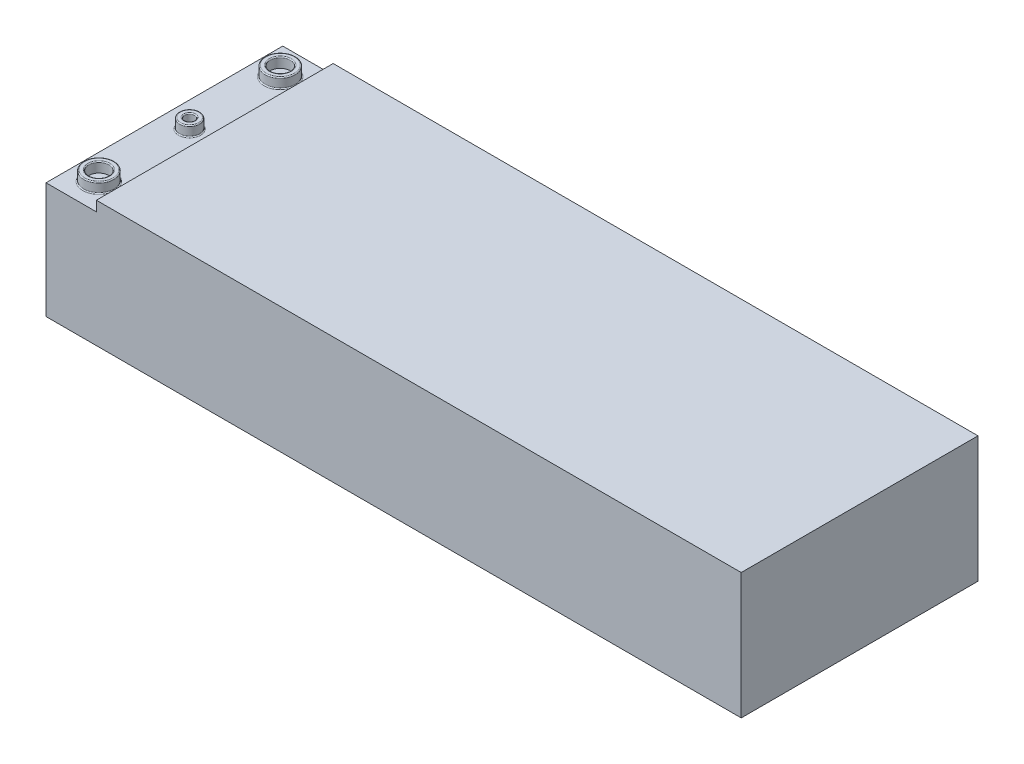
SolidWorks part; units mm, degrees
ref_plane "Front Plane" through (0, 0, 0) normal (0, 0, 1) x (1, 0, 0)
ref_plane "Top Plane" through (0, 0, 0) normal (0, 1, 0) x (1, 0, 0)
ref_plane "Right Plane" through (0, 0, 0) normal (1, 0, 0) x (0, 0, -1)
sketch "Sketch1" plane through (0, 0, 0) normal (0, 1, 0) x (1, 0, 0)
  line L1 (-69, -23.5) -> (69, -23.5)
  line L2 (-69, -23.5) -> (-69, 23.5)
  line L3 (-69, 23.5) -> (69, 23.5)
  line L4 (69, -23.5) -> (69, 23.5)
  line L5 (-69, -23.5) -> (69, 23.5) construction
  line L6 (-69, 23.5) -> (69, -23.5) construction
  point P0 (0, 0)
  dimension "D1" = 47
  dimension "D2" = 138
extrude "Boss-Extrude1" add sketch "Sketch1" along normal blind 25
sketch "Sketch2" plane through (0, 0, 23.5) normal (0, 0, 1) x (1, 0, 0)
  line L1 (-69, 25) -> (-59, 25)
  line L2 (-69, 25) -> (-69, 23)
  line L3 (-69, 23) -> (-59, 23)
  line L4 (-59, 25) -> (-59, 23)
  dimension "D1" = 10
  dimension "D2" = 2
extrude "Cut-Extrude1" cut sketch "Sketch2" against normal through all
sketch "Sketch3" plane through (0, 23, 0) normal (0, 1, 0) x (1, 0, 0)
  line L0 (-1000, 0) -> (49000, 0) construction
  line L1 (-59, 23.5) -> (-59, -23.5) construction
  circle A0 centre (-64, -18) radius 2
  circle A1 centre (-64, -18) radius 3
  circle A2 centre (-64, 0) radius 1
  circle A3 centre (-64, 0) radius 2
  circle A4 centre (-64, 18) radius 2
  circle A5 centre (-64, 18) radius 3
  dimension "D3" = 4
  dimension "D4" = 6
  dimension "D6" = 4
  dimension "D7" = 2
  dimension "D1" = 18
  dimension "D2" = 18
  dimension "D5" = 5
extrude "Boss-Extrude2" add sketch "Sketch3" along normal through all
fillet "Fillet1" radius 0.2 9 edges at (-64, 25, -15) (-64, 25, 21) (-64, 25, 2) (-64, 23, -2) (-64, 23, -21) (-64, 23, 15) (-64, 25, 1) (-64, 25, 20) (-64, 25, -16)
